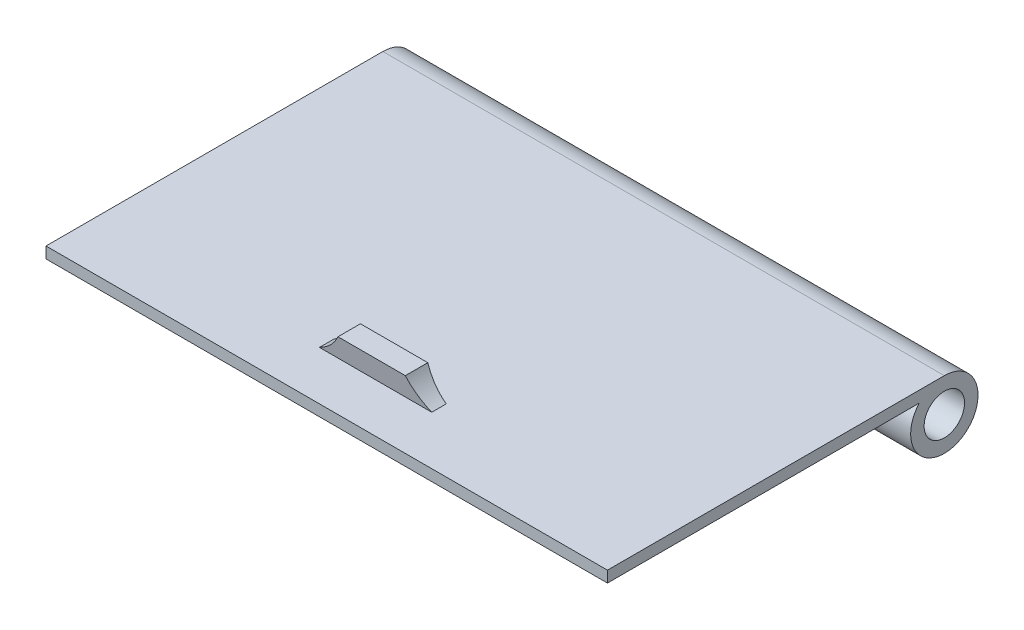
SolidWorks part; units mm, degrees
ref_plane "Front Plane" through (0, 0, 0) normal (0, 0, 1) x (1, 0, 0)
ref_plane "Top Plane" through (0, 0, 0) normal (0, 1, 0) x (1, 0, 0)
ref_plane "Right Plane" through (0, 0, 0) normal (1, 0, 0) x (0, 0, -1)
sketch "Sketch1" plane through (0, 0, 0) normal (0, 1, 0) x (1, 0, 0)
  line L1 (24, 14) -> (-24, 14)
  line L2 (24, 14) -> (24, -14)
  line L3 (24, -14) -> (-24, -14)
  line L4 (-24, 14) -> (-24, -14)
  line L5 (24, 14) -> (-24, -14) construction
  line L6 (24, -14) -> (-24, 14) construction
  point P0 (0, 0)
  dimension "D1" = 48
  dimension "D2" = 28
extrude "Boss-Extrude1" add sketch "Sketch1" along normal blind 1 contours L4 L3 L2 L1
sketch "Sketch2" plane through (0, 1, 0) normal (0, 1, 0) x (1, 0, 0)
  line L8 (25, 15) -> (-25, 15)
  line L9 (-25, 15) -> (-25, -15)
  line L10 (-25, -15) -> (25, -15)
  line L11 (25, -15) -> (25, 15)
  line L12 (25, 15) -> (-25, 15)
  line L13 (-25, 15) -> (-25, -15)
  line L14 (-25, -15) -> (25, -15)
  line L15 (25, -15) -> (25, 15)
  dimension "D1" = 1
extrude "Boss-Extrude2" add sketch "Sketch2" along normal blind 1
sketch "Sketch3" plane through (-25, 0, 0) normal (-1, 0, 0) x (0, 0, 1)
  line L5 (-15, 2) -> (15, 2) construction
  circle A1 centre (-15, -1) radius 3
  point P8 (-15, 2)
  dimension "D1" = 6
extrude "Boss-Extrude3" add sketch "Sketch3" against normal up to surface (50 mm away) up to face at (25, 1.5, 0)
sketch "Sketch4" plane through (-25, 0, 0) normal (-1, 0, 0) x (0, 0, 1)
  circle A0 centre (-15, -1) radius 1.8
  arc A1 (-15, 2) -> (-12.7639, 1) centre (-15, -1) ccw construction
  dimension "D1" = 3.6
extrude "Cut-Extrude1" cut sketch "Sketch4" against normal through all
sketch "Sketch6" plane through (0, 0, 0) normal (1, 0, 0) x (0, 0, -1)
  line L0 (-10.6473, 2) -> (-11, 4)
  line L1 (-15, 2) -> (15, 2) construction
  line L2 (-11, 4) -> (-9, 4)
  line L3 (-9, 4) -> (-9.3527, 2)
  line L4 (-15, 2) -> (-15, 1) construction
  line L5 (-10.6473, 2) -> (-9.3527, 2)
  point P7 (-10, 4)
  dimension "D1" = 2
  dimension "D2" = 2
  dimension "D3" = 80
  dimension "D4" = 80
  dimension "D5" = 5
extrude "Boss-Extrude4" add sketch "Sketch6" along normal mid plane 10
sketch "Sketch8" plane through (0, 0, 15) normal (0, 0, 1) x (1, 0, 0)
  line L0 (5, 4) -> (-5, 4) construction
  line L1 (5, 4) -> (5, 2) construction
  line L2 (3, 4) -> (5, 4)
  line L3 (5, 4) -> (5, 2)
  line L4 (0, 0) -> (0, 5.4382) construction
  line L5 (-24, 0) -> (24, 0) construction
  line L6 (-5, 4) -> (-5, 2)
  line L7 (-3, 4) -> (-5, 4)
  arc A0 (5, 2) -> (3, 4) centre (7.3912, 6.3912) cw
  arc A1 (-5, 2) -> (-3, 4) centre (-7.3912, 6.3912) ccw
  dimension "D1" = 5
  dimension "D2" = 2
extrude "Cut-Extrude2" cut sketch "Sketch8" against normal through all
